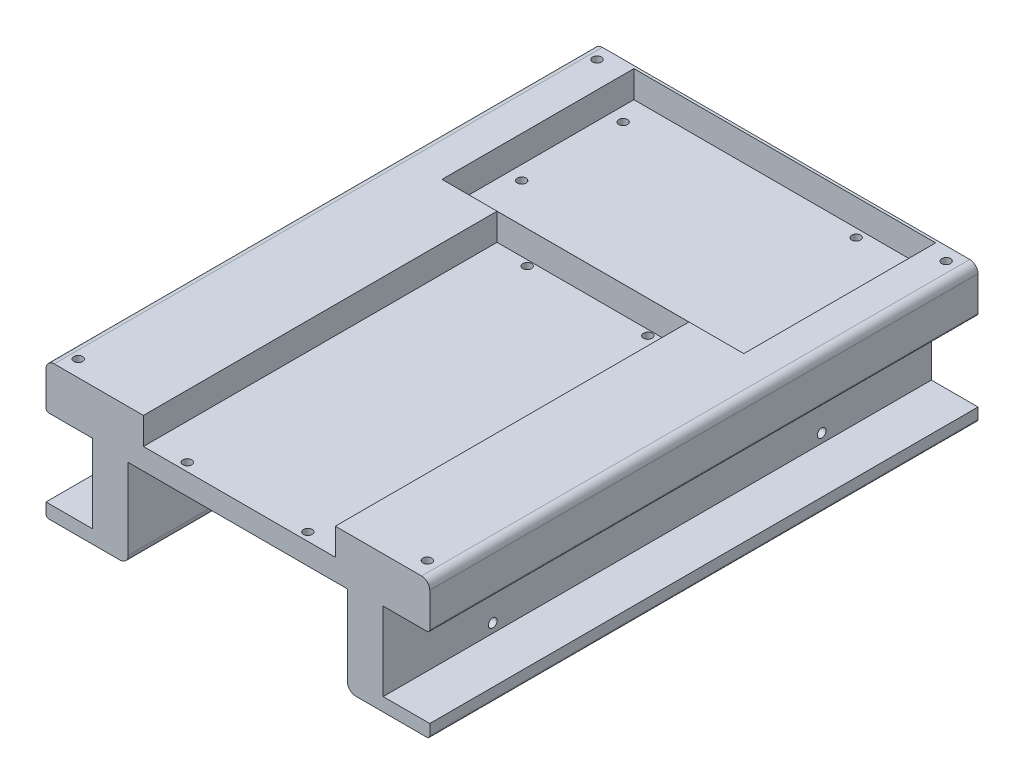
SolidWorks part; units mm, degrees
ref_plane "前视基准面" through (0, 0, 0) normal (0, 0, 1) x (1, 0, 0)
ref_plane "上视基准面" through (0, 0, 0) normal (0, 1, 0) x (1, 0, 0)
ref_plane "右视基准面" through (0, 0, 0) normal (1, 0, 0) x (0, 0, -1)
other "Configuration Table"
sketch "草图1" plane through (0, 0, 0) normal (0, 0, 1) x (1, 0, 0)
  line L0 (-40.5405, -50.1772) -> (-40.5405, -17.8003)
  line L1 (-70.5405, -0.1772) -> (69.4595, -0.1772)
  line L2 (-70.5405, -0.1772) -> (-70.5405, -50.1772)
  line L4 (69.4595, -0.1772) -> (69.4595, -50.1772)
  line L5 (-40.5405, -17.8003) -> (39.4595, -17.8003)
  line L6 (39.4595, -17.8003) -> (39.4595, -50.1772)
  line L7 (-70.5405, -50.1772) -> (-40.5405, -50.1772)
  line L8 (39.4595, -50.1772) -> (69.4595, -50.1772)
  dimension "D1" = 30
  dimension "D2" = 140
  dimension "D3" = 80
  dimension "D4" = 50
extrude "凸台-拉伸2" add sketch "草图1" along normal mid plane 200
sketch "草图4" plane through (0, 0, 0) normal (0, 1, 0) x (1, 0, 0)
  line L1 (-55.0938, 99.0241) -> (55, 99.0241)
  line L2 (-55.0938, 99.0241) -> (-55.0938, 29.0241)
  line L3 (-55.0938, 29.0241) -> (55, 29.0241)
  line L4 (55, 99.0241) -> (55, 29.0241)
  line L5 (-35, 29) -> (35, 29)
  line L6 (-35, 29) -> (-35, -100.3512)
  line L7 (-35, -100.3512) -> (35, -100.3512)
  line L8 (35, 29) -> (35, -100.3512)
  point P8 (0, 0)
  point P9 (0, 0)
  point P10 (0, 0)
  point P11 (0, 0)
  point P12 (0, 0)
  point P13 (0, 0)
  point P14 (0, 0)
  point P15 (0, 0)
  point P16 (0, 0)
  point P17 (0, 0)
  point P18 (0, 0)
  point P19 (0, 0)
  point P20 (0, 0)
  point P21 (0, 0)
  point P22 (0, 0)
  point P23 (0, 0)
  point P24 (0, 0)
  point P25 (0, 0)
  point P26 (0, 0)
  point P27 (0, 0)
  point P28 (0, 0)
  point P29 (0, 0)
  point P30 (0, 0)
  point P31 (0, 0)
  point P32 (0, 0)
  point P33 (0, 0)
extrude "切除-拉伸1" cut sketch "草图4" against normal blind 10
sketch "草图5" plane through (0, 0, 0) normal (0, 1, 0) x (1, 0, 0)
  circle A0 centre (29, 96) radius 1.6
  circle A1 centre (-50, 53) radius 1.6
  circle A2 centre (28, 35) radius 1.6
  circle A3 centre (-50, 90) radius 1.6
  circle A4 centre (-22, 27) radius 1.6
  circle A5 centre (22, 27) radius 1.6
  circle A6 centre (-22, -97) radius 1.6
  circle A7 centre (22, -97) radius 1.6
  circle A8 centre (-64.6934, 95.1628) radius 1.6
  circle A9 centre (62.6689, 95.1628) radius 1.6
  circle A10 centre (62.6689, -94.069) radius 1.6
  circle A11 centre (-64.6934, -94.069) radius 1.6
  point P2 (0, 0)
  point P5 (0, 0)
  point P8 (0, 0)
  point P11 (0, 0)
  point P12 (0, 0)
  point P13 (0, 0)
  point P14 (0, 0)
  point P15 (0, 0)
  point P16 (0, 0)
  point P17 (0, 0)
  point P18 (0, 0)
  point P19 (0, 0)
  point P20 (0, 0)
  point P21 (0, 0)
  point P22 (0, 0)
  point P23 (0, 0)
  point P26 (0, 0)
  point P29 (0, 0)
  point P32 (0, 0)
  point P33 (0, 0)
  point P36 (0, 0)
  point P37 (0, 0)
  point P38 (0, 0)
  point P39 (0, 0)
  point P42 (-64.6934, 107.2359)
  point P45 (62.6689, 107.2359)
  point P48 (62.6689, -109.1228)
  point P51 (-64.6934, -109.1228)
  point P52 (0, 0)
  point P53 (-64.6934, -109.1228)
  point P54 (-64.6934, 93)
  point P55 (-64.6934, 95.1628)
  point P56 (62.6689, 95.1628)
  point P57 (62.6689, -94.069)
  point P58 (-64.6934, -94.069)
  point P59 (0, 0)
  point P60 (0, 0)
  point P61 (0, 0)
  point P62 (0, 0)
  point P63 (0, 0)
  point P64 (0, 0)
  point P65 (0, 0)
  point P66 (0, 0)
  point P67 (0, 0)
  point P68 (0, 0)
  point P69 (0, 0)
  point P70 (0, 0)
  point P71 (0, 0)
  point P72 (0, 0)
  point P73 (0, 0)
  point P74 (0, 0)
  point P75 (0, 0)
  point P76 (0, 0)
extrude "切除-拉伸2" cut sketch "草图5" against normal blind 22
sketch "草图6" plane through (0, 0, 0) normal (0, 0, 1) x (1, 0, 0)
  line L0 (69.4595, -50.1772) -> (69.4595, -0.1772) construction
  line L1 (-70.5405, -0.1772) -> (-70.5405, -50.1772) construction
  line L2 (-70.5405, -16.6937) -> (-53.5405, -16.6937)
  line L3 (-70.5405, -16.6937) -> (-70.5405, -45.2937)
  line L4 (-70.5405, -45.2937) -> (-53.5405, -45.2937)
  line L5 (-53.5405, -16.6937) -> (-53.5405, -45.2937)
  line L6 (52.4595, -16.6937) -> (52.4595, -45.2937)
  line L7 (69.4595, -45.2937) -> (52.4595, -45.2937)
  line L8 (69.4595, -16.6937) -> (69.4595, -45.2937)
  line L9 (69.4595, -16.6937) -> (52.4595, -16.6937)
extrude "切除-拉伸3" cut sketch "草图6" against normal through all both and the other way through all
sketch "草图7" plane through (0, 0, 0) normal (1, 0, 0) x (0, 0, -1)
  circle A0 centre (-60, -20) radius 1.6
  circle A1 centre (-60, -42) radius 1.6
  circle A2 centre (60, -42) radius 1.6
  circle A3 centre (60, -20) radius 1.6
  point P6 (0, 0)
  point P7 (0, 0)
  point P8 (0, 0)
  point P9 (0, 0)
extrude "切除-拉伸4" cut sketch "草图7" against normal mid plane 169
fillet "圆角1" radius 1 4 edges at (69.4595, -16.6937, 0) (-70.5405, -16.6937, 0) (-70.5405, -50.1772, 0) (69.4595, -50.1772, 0)
fillet "圆角2" radius 3 4 edges at (-70.5405, -0.1772, 0) (69.4595, -0.1772, 0) (-40.5405, -50.1772, 0) (39.4595, -50.1772, 0)
